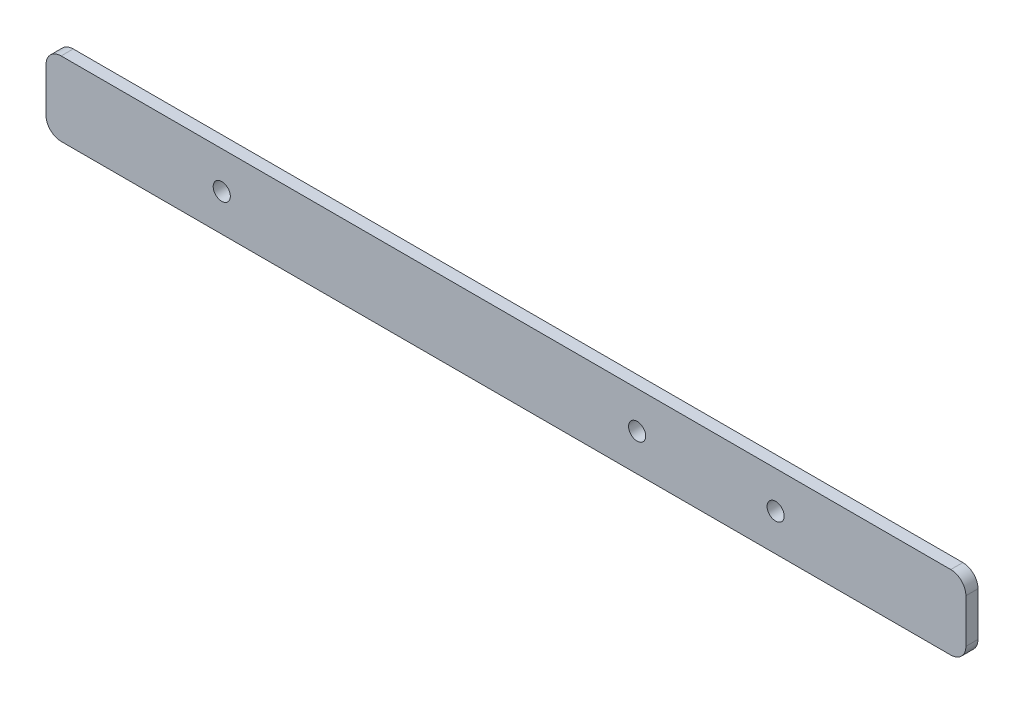
SolidWorks part; units mm, degrees
material "Acrylic (Medium-high impact)"
ref_plane "Front Plane" through (0, 0, 0) normal (0, 0, 1) x (1, 0, 0)
ref_plane "Top Plane" through (0, 0, 0) normal (0, 1, 0) x (1, 0, 0)
ref_plane "Right Plane" through (0, 0, 0) normal (1, 0, 0) x (0, 0, -1)
sketch "Sketch1" plane through (0, 0, 0) normal (0, 0, 1) x (1, 0, 0)
  line L1 (0, 0) -> (241.3, 0)
  line L2 (0, 0) -> (0, 19.431)
  line L3 (0, 19.431) -> (241.3, 19.431)
  line L4 (241.3, 0) -> (241.3, 19.431)
  dimension "D1" = 241.3
  dimension "D2" = 19.431
extrude "Boss-Extrude1" add sketch "Sketch1" along normal blind 3.175
hole_wizard "#8 Clearance Hole1" positions "Sketch2" profile "Sketch3" hole size "#8" standard "ANSI Inch" end condition through all
sketch "Sketch2" plane through (0, 0, 3.175) normal (0, 0, 1) x (1, 0, 0)
  line L0 (0, 9.7155) -> (241.3, 9.7155) construction
  line L1 (0, 19.431) -> (0, 0) construction
  line L2 (241.3, 0) -> (241.3, 19.431) construction
  line L3 (264.033, 90.6927) -> (264.033, -71.2617) construction
  point P0 (46.101, 9.7155)
  point P2 (155.067, 9.7155)
  point P24 (264.033, 9.7155)
  point P26 (191.389, 9.7155)
  dimension "D1" = 108.966
  dimension "D2" = 264.033
  dimension "D3" = 217.932
  dimension "D4" = 36.322
sketch "Sketch3" plane through (46.101, 9.7155, 3.175) normal (1, 0, 0) x (0, -1, 0)
  line L0 (0, 0) -> (0, 3.175)
  line L1 (0, 3.175) -> (2.2479, 3.175)
  line L2 (2.2479, 3.175) -> (2.2479, 0)
  line L5 (2.2479, 0) -> (0, 0)
  line L11 (0, -6.35) -> (0, 107.95) construction
  dimension "Thru Hole Dia." = 4.4958
  dimension "Thru Hole Depth" = 3.175
fillet "Fillet1" radius 3.9688 4 edges at (0, 19.431, 1.5875) (0, 0, 1.5875) (241.3, 0, 1.5875) (241.3, 19.431, 1.5875)
